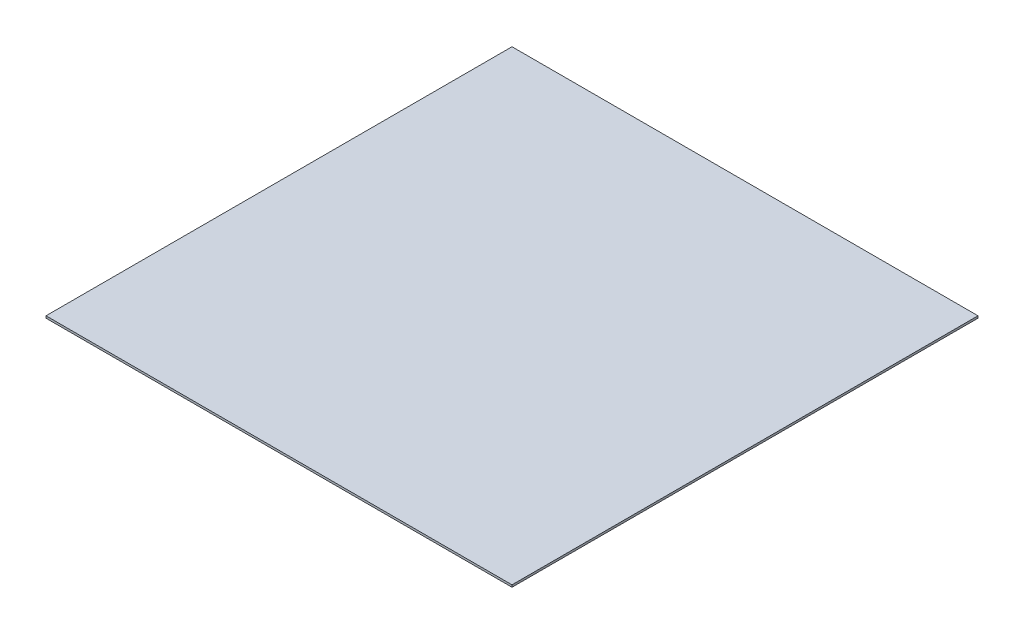
SolidWorks part; units mm, degrees
material "Teak"
ref_plane "Front Plane" through (0, 0, 0) normal (0, 0, 1) x (1, 0, 0)
ref_plane "Top Plane" through (0, 0, 0) normal (0, 1, 0) x (1, 0, 0)
ref_plane "Right Plane" through (0, 0, 0) normal (1, 0, 0) x (0, 0, -1)
sketch "Sketch1" plane through (0, 0, 0) normal (0, 1, 0) x (1, 0, 0)
  line L1 (-609.6, -609.6) -> (609.6, -609.6)
  line L2 (-609.6, -609.6) -> (-609.6, 609.6)
  line L3 (-609.6, 609.6) -> (609.6, 609.6)
  line L4 (609.6, -609.6) -> (609.6, 609.6)
  line L5 (-609.6, -609.6) -> (609.6, 609.6) construction
  line L6 (-609.6, 609.6) -> (609.6, -609.6) construction
  point P0 (0, 0)
  dimension "D1" = 1219.2
extrude "Boss-Extrude1" add sketch "Sketch1" along normal blind 5.5562
